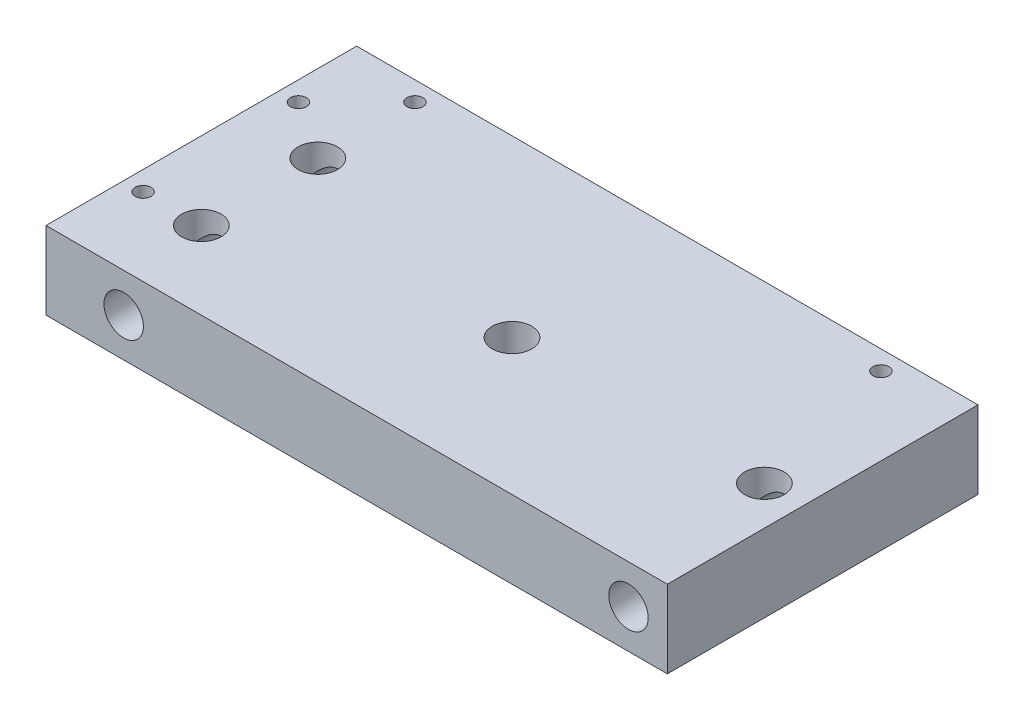
SolidWorks part; units mm, degrees
ref_plane "Front Plane" through (0, 0, 0) normal (0, 0, 1) x (1, 0, 0)
ref_plane "Top Plane" through (0, 0, 0) normal (0, 1, 0) x (1, 0, 0)
ref_plane "Right Plane" through (0, 0, 0) normal (1, 0, 0) x (0, 0, -1)
sketch "Sketch1" plane through (0, 0, 0) normal (0, 1, 0) x (1, 0, 0)
  line L1 (-100, 50) -> (100, 50)
  line L2 (-100, 50) -> (-100, -50)
  line L3 (-100, -50) -> (100, -50)
  line L4 (100, 50) -> (100, -50)
  line L5 (-100, 50) -> (100, -50) construction
  line L6 (-100, -50) -> (100, 50) construction
  point P0 (0, 0)
  dimension "D1" = 200
  dimension "D2" = 100
extrude "Boss-Extrude1" add sketch "Sketch1" along normal blind 25
sketch "Sketch2" plane through (0, 0, 50) normal (0, 0, 1) x (1, 0, 0)
  line L0 (-100, 12.5) -> (100, 12.5) construction
  line L1 (-100, 25) -> (-100, 0) construction
  line L2 (100, 25) -> (100, 0) construction
  line L3 (-75, 25) -> (-75, 0) construction
  line L4 (-100, 25) -> (100, 25) construction
  line L5 (-100, 0) -> (100, 0) construction
  line L6 (87.5, 25) -> (87.5, 0) construction
  circle A0 centre (-75, 12.5) radius 6.35
  circle A1 centre (87.5, 12.5) radius 6.35
  dimension "D3" = 12.7
  dimension "D4" = 12.7
  dimension "D1" = 25
  dimension "D2" = 12.5
extrude "Cut-Extrude1" cut sketch "Sketch2" against normal blind 87.5
sketch "Sketch3" plane through (0, 25, 0) normal (0, 1, 0) x (1, 0, 0)
  line L0 (-75, 50) -> (-75, -50) construction
  line L1 (100, 50) -> (-100, 50) construction
  line L2 (-100, -50) -> (100, -50) construction
  line L3 (87.5, 50) -> (87.5, -50) construction
  line L4 (-100, 50) -> (-100, -50) construction
  line L5 (100, -50) -> (100, 50) construction
  line L6 (-87.5, 12.5) -> (100, 12.5) construction
  line L7 (100, -50) -> (-87.5, -50)
  line L8 (100, -50) -> (100, 37.5)
  line L9 (100, 37.5) -> (-87.5, 37.5)
  line L10 (-87.5, -50) -> (-87.5, 37.5)
  line L11 (-87.5, -25) -> (100, -25) construction
  line L12 (-87.5, -6.25) -> (100, -6.25) construction
  circle A0 centre (-75, 12.5) radius 6.35
  circle A1 centre (-75, -25) radius 6.35
  circle A2 centre (87.5, -6.25) radius 6.35
  dimension "D7" = 12.7
  dimension "D8" = 12.7
  dimension "D9" = 12.7
  dimension "D1" = 25
  dimension "D2" = 12.5
  dimension "D3" = 12.5
  dimension "D4" = 12.5
  dimension "D5" = 25
  dimension "D6" = 25
extrude "Cut-Extrude2" cut sketch "Sketch3" against normal blind 19 contours A0 | A1 | A2
sketch "Sketch4" plane through (0, 25, 0) normal (0, 1, 0) x (1, 0, 0)
  line L0 (100, 50) -> (-100, 50) construction
  line L1 (-87.5, 37.5) -> (100, 37.5)
  line L2 (-87.5, 37.5) -> (-87.5, -50)
  line L3 (-87.5, -50) -> (100, -50)
  line L4 (100, 37.5) -> (100, -50)
  line L5 (-100, 50) -> (-100, -50) construction
  line L6 (-87.5, -6.25) -> (100, -6.25) construction
  line L7 (6.25, 37.5) -> (6.25, -50) construction
  circle A0 centre (6.25, -6.25) radius 6.35
  dimension "D3" = 12.7
  dimension "D1" = 12.5
  dimension "D2" = 12.5
extrude "Cut-Extrude3" cut sketch "Sketch4" against normal up to next contours A0
sketch "Sketch5" plane through (0, 0, 0) normal (0, -1, 0) x (-1, 0, 0)
  line L0 (-6.25, -50) -> (-6.25, 50) construction
  line L1 (100, -50) -> (-100, -50) construction
  line L2 (-100, 50) -> (100, 50) construction
  line L3 (-6.25, -18.2561) -> (-6.25, 7.1439) construction
  line L4 (-9.425, -18.2561) -> (-9.425, 7.1439)
  line L5 (-3.075, -18.2561) -> (-3.075, 7.1439)
  circle A1 centre (-6.25, -6.25) radius 6.35
  arc A2 (-9.425, -18.2561) -> (-3.075, -18.2561) centre (-6.25, -18.2561) ccw
  arc A3 (-3.075, 7.1439) -> (-9.425, 7.1439) centre (-6.25, 7.1439) ccw
  point P11 (-6.25, -5.5561)
  circle M1 centre (-6.25, -6.25) radius 6.35
  dimension "D1" = 6.35
  dimension "D2" = 25.4
extrude "Cut-Extrude4" cut sketch "Sketch5" against normal blind 6.35 contours L5 A3 L4 M1 | L4 A2 L5 M1
sketch "Sketch6" plane through (0, 25, 0) normal (0, 1, 0) x (1, 0, 0)
  line L0 (100, 50) -> (-100, 50) construction
  line L1 (-87.5, 37.5) -> (100, 37.5)
  line L2 (-87.5, 37.5) -> (-87.5, -50)
  line L3 (-87.5, -50) -> (100, -50)
  line L4 (100, 37.5) -> (100, -50)
  line L5 (-100, 50) -> (-100, -50) construction
  line L6 (-100, 43.75) -> (100, 43.75) construction
  line L7 (100, -50) -> (100, 50) construction
  line L8 (-93.75, 50) -> (-93.75, -50) construction
  line L9 (-100, -50) -> (100, -50) construction
  dimension "D1" = 12.5
  dimension "D2" = 12.5
  dimension "D3" = 6.25
  dimension "D4" = 6.25
sketch "Sketch7" plane through (0, 25, 0) normal (0, 1, 0) x (1, 0, 0)
  line L0 (-100, 43.75) -> (100, 43.75) construction
  line L1 (-100, 50) -> (-100, -50) construction
  line L2 (100, -50) -> (100, 50) construction
  line L3 (-93.75, 50) -> (-93.75, -50) construction
  line L4 (-100, -50) -> (100, -50) construction
  line L5 (100, 50) -> (-100, 50) construction
  point P0 (-75, 43.75)
  point P1 (75, 43.75)
  point P8 (-93.75, 25)
  point P9 (-93.75, -25)
  dimension "D1" = 25
  dimension "D2" = 25
  dimension "D3" = 25
  dimension "D4" = 25
hole_wizard "1/4-20 Tapped Hole1" positions "3DSketch1" profile "Sketch8" tap size "1/4-20" standard "ANSI Inch" end condition up to next
sketch3d "3DSketch1"
  point P0 (-75, 25, -43.75)
  point P3 (75, 25, -43.75)
  point P6 (-93.75, 25, -25)
  point P9 (-93.75, 25, 25)
sketch "Sketch8" plane through (-75, 25, -43.75) normal (1, 0, 0) x (0, 0, 1)
  line L0 (0, 0) -> (0, 25)
  line L1 (0, 25) -> (2.5527, 25)
  line L2 (2.5527, 25) -> (2.5527, 0)
  line L5 (2.5527, 0) -> (0, 0)
  line L11 (0, -6.35) -> (0, 107.95) construction
  dimension "Thru Tap Drill Dia." = 5.1054
  dimension "Thru Tap Drill Depth" = 25
cosmetic thread "Hole Thread1" parameters "D2"=6.35
cosmetic thread "Hole Thread2" parameters "D2"=6.35
cosmetic thread "Hole Thread3" parameters "D2"=6.35
cosmetic thread "Hole Thread4" parameters "D2"=6.35
